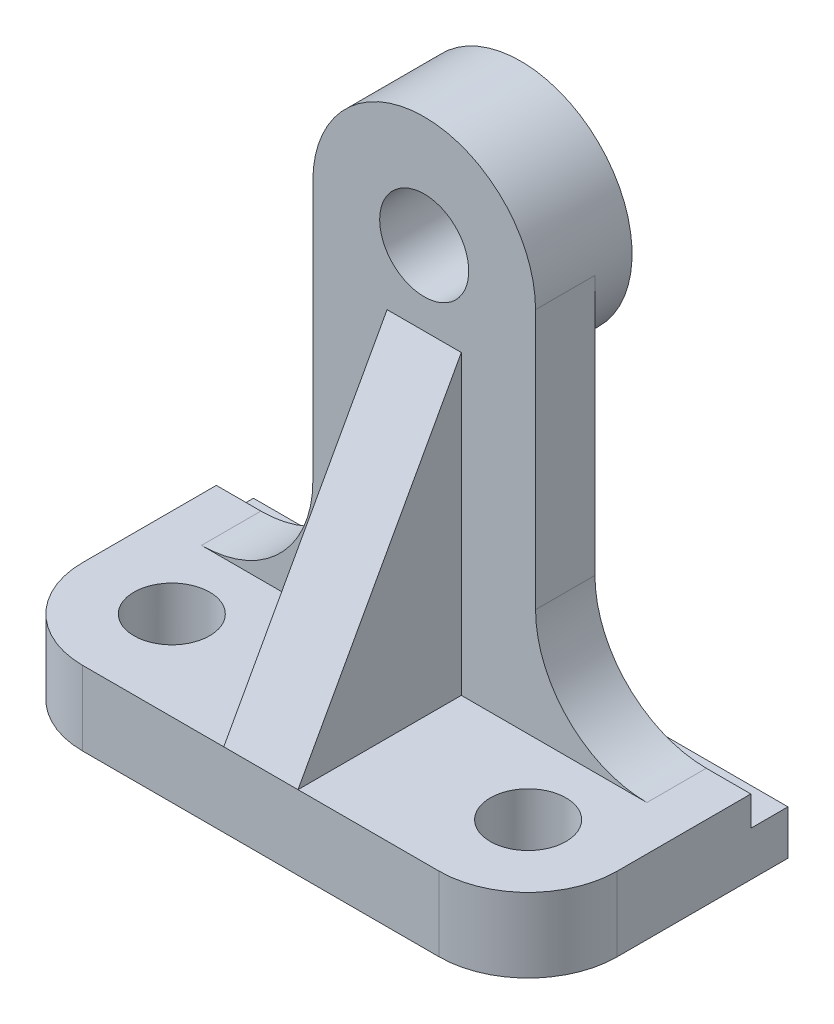
SolidWorks part; units mm, degrees
ref_plane "Front Plane" through (0, 0, 0) normal (0, 0, 1) x (1, 0, 0)
ref_plane "Top Plane" through (0, 0, 0) normal (0, 1, 0) x (1, 0, 0)
ref_plane "Right Plane" through (0, 0, 0) normal (1, 0, 0) x (0, 0, -1)
sketch "Sketch1" plane through (0, 0, 0) normal (0, 1, 0) x (1, 0, 0)
  line L1 (-36, -17.5) -> (36, -17.5)
  line L2 (-36, -17.5) -> (-36, 17.5)
  line L3 (-36, 17.5) -> (36, 17.5)
  line L4 (36, -17.5) -> (36, 17.5)
  line L5 (-36, -17.5) -> (36, 17.5) construction
  line L6 (-36, 17.5) -> (36, -17.5) construction
  point P0 (0, 0)
  dimension "D1" = 35
  dimension "D2" = 72
extrude "Boss-Extrude1" add sketch "Sketch1" along normal blind 10
fillet "Fillet1" radius 12 2 edges at (36, 5, 17.5) (-36, 5, 17.5)
sketch "Sketch3" plane through (36, 0, 0) normal (1, 0, 0) x (0, 0, -1)
  line L1 (17.5, 10) -> (12.5, 10)
  line L2 (17.5, 10) -> (17.5, 6)
  line L3 (17.5, 6) -> (12.5, 6)
  line L4 (12.5, 10) -> (12.5, 6)
  dimension "D1" = 5
  dimension "D2" = 4
extrude "Cut-Extrude1" cut sketch "Sketch3" against normal through all
sketch "Sketch4" plane through (0, 0, -12.5) normal (0, 0, -1) x (-1, 0, 0)
  line L0 (-15, 10) -> (15, 10)
  line L1 (36, 10) -> (-36, 10) construction
  line L2 (15, 10) -> (15, 60)
  line L3 (-15, 60) -> (-15, 10)
  arc A0 (15, 60) -> (-15, 60) centre (0, 60) ccw
  circle A1 centre (0, 60) radius 6
  dimension "D1" = 12
  dimension "D2" = 15
  dimension "D3" = 50
extrude "Boss-Extrude2" add sketch "Sketch4" against normal blind 8
fillet "Fillet2" radius 15 2 edges at (-15, 10, -8.5) (15, 10, -8.5)
hole_wizard "M12 Tapped Hole1" positions "Sketch5" profile "Sketch6" tap size "M12" standard "DIN" end condition up to next
sketch "Sketch5" plane through (0, 10, 0) normal (0, 1, 0) x (1, 0, 0)
  point P0 (-24, -5.5)
  point P3 (24, -5.5)
sketch "Sketch6" plane through (-24, 10, 5.5) normal (1, 0, 0) x (0, 0, 1)
  line L0 (0, 0) -> (0, 10)
  line L1 (0, 10) -> (5.1, 10)
  line L2 (5.1, 10) -> (5.1, 0)
  line L5 (5.1, 0) -> (0, 0)
  line L11 (0, -6.35) -> (0, 107.95) construction
  dimension "Thru Tap Drill Dia." = 10.2
  dimension "Thru Tap Drill Depth" = 10
cosmetic thread "Hole Thread1" parameters "D2"=12
cosmetic thread "Hole Thread2" parameters "D2"=12
sketch "Sketch7" plane through (0, 0, -12.5) normal (0, 0, -1) x (-1, 0, 0)
  circle A0 centre (0, 60) radius 15
  circle A1 centre (0, 60) radius 6 construction
  circle A2 centre (0, 60) radius 6
  dimension "D1" = 30
extrude "Boss-Extrude3" add sketch "Sketch7" along normal blind 5
sketch "Sketch8" plane through (0, 0, 0) normal (1, 0, 0) x (0, 0, -1)
  line L2 (4.5, 60) -> (4.5, 25) construction
  line L3 (4.5, 50) -> (-17.5, 10)
  dimension "D1" = 40
rib "Rib1" sketch "Sketch8" sketch "Sketch8" thickness 10 extrusion direction parallel to sketch draft on no parameters "D1"=10
